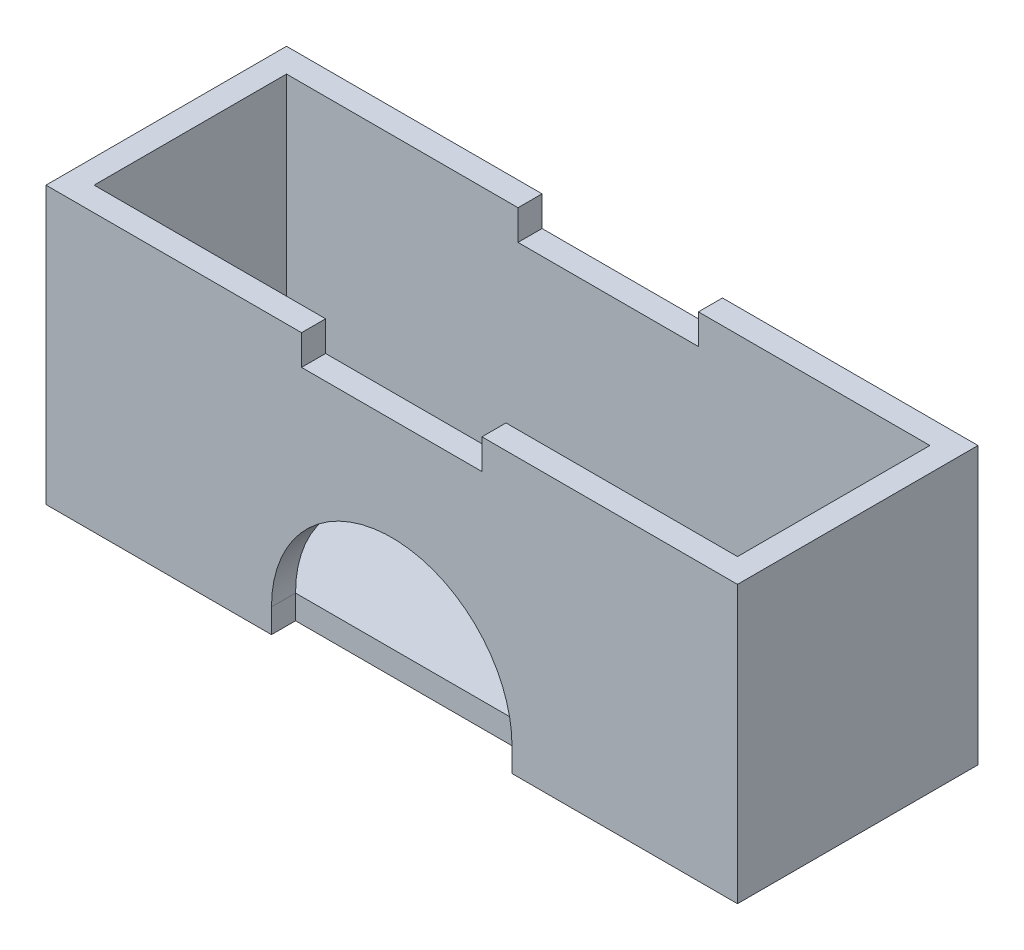
SolidWorks part; units mm, degrees
ref_plane "Front Plane" through (0, 0, 0) normal (0, 0, 1) x (1, 0, 0)
ref_plane "Top Plane" through (0, 0, 0) normal (0, 1, 0) x (1, 0, 0)
ref_plane "Right Plane" through (0, 0, 0) normal (1, 0, 0) x (0, 0, -1)
sketch "Sketch1" plane through (0, 0, 0) normal (0, 1, 0) x (1, 0, 0)
  line L1 (0, 0) -> (146.05, 0)
  line L2 (0, 0) -> (0, 50.8)
  line L3 (0, 50.8) -> (146.05, 50.8)
  line L4 (146.05, 0) -> (146.05, 50.8)
  dimension "D1" = 146.05
  dimension "D2" = 50.8
extrude "Boss-Extrude1" add sketch "Sketch1" along normal blind 58.42
shell "Shell1" thickness 5.08
sketch "Sketch2" plane through (0, 0, 0) normal (0, 0, 1) x (1, 0, 0)
  line L0 (0, 0) -> (146.05, 0) construction
  line L1 (47.625, 0) -> (98.425, 0)
  line L2 (47.625, 0) -> (47.625, 5.08)
  line L3 (47.625, 5.08) -> (98.425, 5.08)
  line L4 (98.425, 0) -> (98.425, 5.08)
  line L6 (73.025, 5.08) -> (73.025, 58.42) construction
  line L7 (0, 58.42) -> (146.05, 58.42) construction
  arc A0 (47.625, 5.08) -> (98.425, 5.08) centre (73.025, 5.08) cw
  dimension "D1" = 5.08
  dimension "D2" = 50.8
extrude "Cut-Extrude2" cut sketch "Sketch2" against normal blind 5.08 contours L3 L6 A0 | L6 L3 A0 | L0 L4 L3 L2
sketch "Sketch4" plane through (0, 58.42, 0) normal (0, 1, 0) x (1, 0, 0)
  line L0 (73.025, 50.8) -> (73.025, 0) construction
  line L1 (53.975, 50.8) -> (92.075, 50.8)
  line L2 (53.975, 50.8) -> (53.975, 0)
  line L3 (53.975, 0) -> (92.075, 0)
  line L4 (92.075, 50.8) -> (92.075, 0)
  line L5 (146.05, 50.8) -> (0, 50.8) construction
  line L6 (0, 0) -> (146.05, 0) construction
  line L7 (73.025, 50.8) -> (73.025, 0) construction
  dimension "D1" = 38.1
extrude "Cut-Extrude3" cut sketch "Sketch4" against normal blind 6.35
